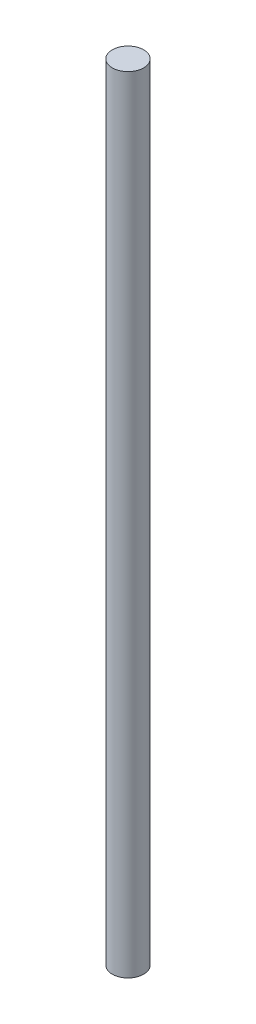
SolidWorks part; units mm, degrees
ref_plane "Front Plane" through (0, 0, 0) normal (0, 0, 1) x (1, 0, 0)
ref_plane "Top Plane" through (0, 0, 0) normal (0, 1, 0) x (1, 0, 0)
ref_plane "Right Plane" through (0, 0, 0) normal (1, 0, 0) x (0, 0, -1)
sketch "Sketch1" plane through (0, 0, 0) normal (0, 1, 0) x (1, 0, 0)
  circle A0 centre (0, 0) radius 4
extrude "Boss-Extrude1" add sketch "Sketch1" along normal blind 200
